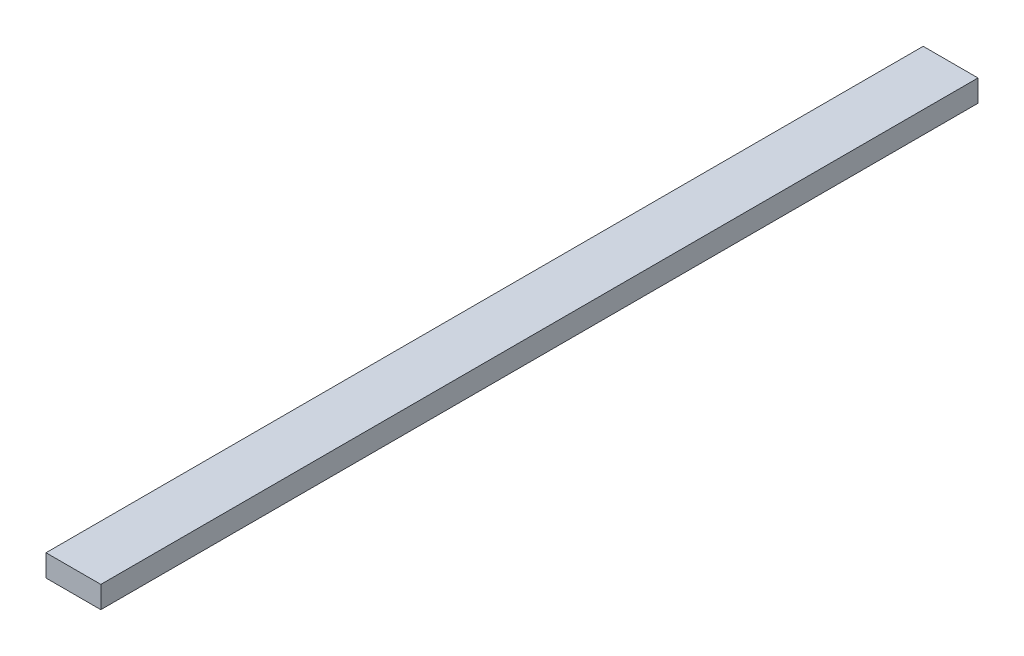
SolidWorks part; units mm, degrees
ref_plane "Front Plane" through (0, 0, 0) normal (0, 0, 1) x (1, 0, 0)
ref_plane "Top Plane" through (0, 0, 0) normal (0, 1, 0) x (1, 0, 0)
ref_plane "Right Plane" through (0, 0, 0) normal (1, 0, 0) x (0, 0, -1)
sketch "Sketch1" plane through (0, 0, 0) normal (0, 1, 0) x (1, 0, 0)
  line L1 (0, 0) -> (250, 0)
  line L2 (0, 0) -> (0, 4000)
  line L3 (0, 4000) -> (250, 4000)
  line L4 (250, 0) -> (250, 4000)
extrude "Boss-Extrude1" add sketch "Sketch1" along normal blind 100
